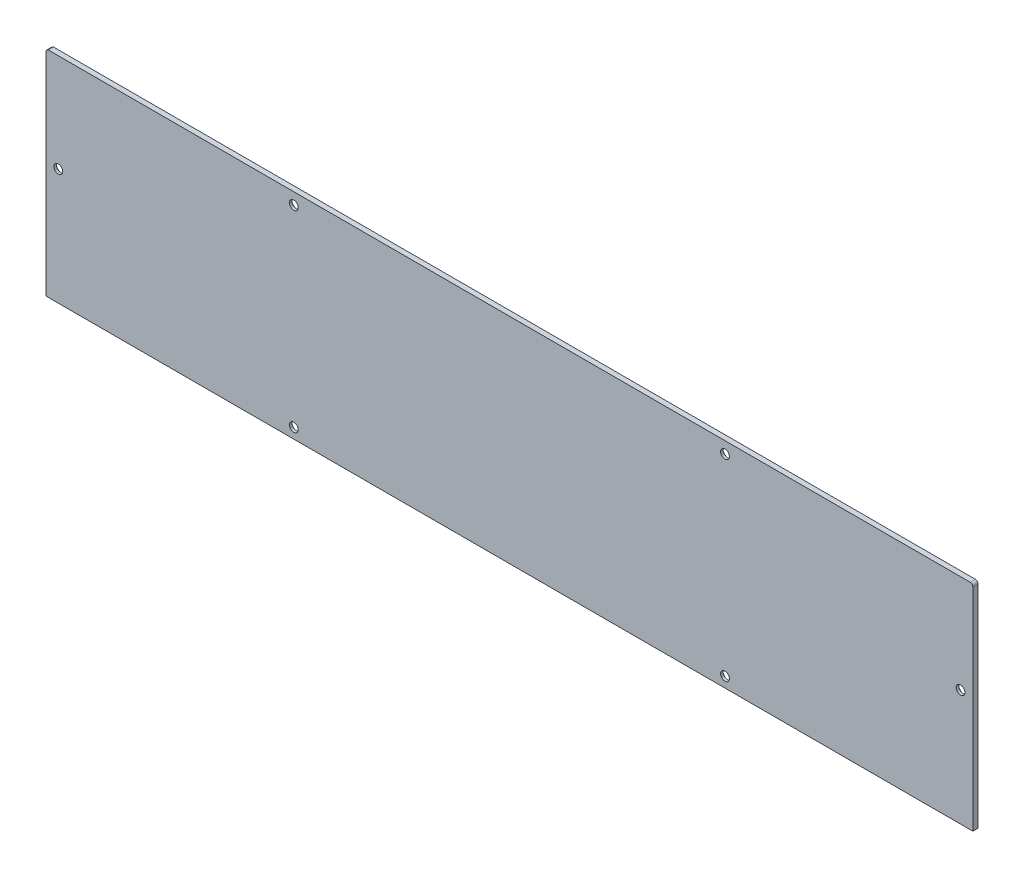
SolidWorks part; units mm, degrees
material "6061 合金"
ref_plane "前视基准面" through (0, 0, 0) normal (0, 0, 1) x (1, 0, 0)
ref_plane "上视基准面" through (0, 0, 0) normal (0, 1, 0) x (1, 0, 0)
ref_plane "右视基准面" through (0, 0, 0) normal (1, 0, 0) x (0, 0, -1)
sketch "草图1" plane through (0, 0, 222.7245) normal (0, 0, -1) x (-1, 0, 0)
  line L0 (282.7502, -10) -> (-76.2519, -10) construction
  line L1 (-76.2519, 70) -> (-76.2519, -2.5) construction
  line L2 (282.7502, -8.05) -> (282.7502, 70) construction
  line L4 (-76.2519, -10) -> (282.7502, -10)
  line L5 (282.7502, 70) -> (282.7502, -10)
  line L6 (279.7502, 73) -> (-73.2519, 73)
  line L7 (-76.2519, -10) -> (-76.2519, 70)
  arc A2 (282.7502, 70) -> (279.7502, 73) centre (279.7502, 70) ccw
  arc A3 (-73.2519, 73) -> (-76.2519, 70) centre (-73.2519, 70) ccw
  arc A4 (-73.2519, 73) -> (-76.2519, 70) centre (-73.2519, 70) ccw construction
  arc A5 (282.7502, 70) -> (279.7502, 73) centre (279.7502, 70) ccw construction
extrude "凸台-拉伸1" add sketch "草图1" along normal blind 2
sketch "草图2" plane through (0, 0, 220.7245) normal (0, 0, 1) x (1, 0, 0)
  line L0 (71.5019, 35) -> (71.5019, 68.5) construction
  line L1 (71.5019, 68.5) -> (-19.7492, 68.5) construction
  line L2 (-19.7492, 68.5) -> (-186.7492, 68.5) construction
  line L3 (-186.7492, 68.5) -> (-278.0002, 68.5) construction
  line L4 (-278.0002, 68.5) -> (-278.0002, 35) construction
  circle A1 centre (-19.7492, 68.5) radius 1.25 construction
  circle A4 centre (-278.0002, 35) radius 1.25
  circle A5 centre (-186.7492, 68.5) radius 1.25
  circle A6 centre (-19.7492, 68.5) radius 1.0541
  circle A7 centre (71.5019, 35) radius 1.25
  circle A11 centre (-278.0002, 35) radius 1.0974 construction
  circle A14 centre (71.5019, 35) radius 1.25 construction
hole_wizard "打孔尺寸(%根据)内六角圆柱头螺钉的类型2" positions "3D草图1" profile "草图3" counterbore size "M3" standard "GB"
sketch3d "3D草图1"
  point P0 (71.5019, 35, 220.7245)
  point P3 (-19.7492, 68.5, 220.7245)
  point P6 (-186.7492, 68.5, 220.7245)
  point P9 (-278.0002, 35, 220.7245)
sketch "草图3" plane through (71.5019, 35, 220.7245) normal (1, 0, 0) x (0, 1, 0)
  line L0 (0, 0) -> (0, 8.5215)
  line L1 (0, 8.5215) -> (1.7, 7.5)
  line L2 (1.7, 7.5) -> (1.7, 1)
  line L3 (1.7, 1) -> (3, 1)
  line L4 (3, 1) -> (3, 0)
  line L5 (3, 0) -> (0, 0)
  line L10 (0, 8.5215) -> (-1.7, 7.5) construction
  line L11 (0, -6.35) -> (0, 107.95) construction
  dimension "孔直径" = 3.4
  dimension "孔深度" = 7.5
  dimension "柱形沉头孔直径" = 6
  dimension "柱形沉头孔深度" = 1
  dimension "导头角度" = 118
sketch "草图4" plane through (0, 0, 220.7245) normal (0, 0, -1) x (-1, 0, 0)
  line L4 (-76.2519, 70) -> (-76.2519, -10)
  line L5 (-76.2519, -10) -> (282.7502, -10)
  line L6 (282.7502, -10) -> (282.7502, 70)
  line L7 (279.7502, 73) -> (-73.2519, 73)
  line L8 (-76.2519, 70) -> (-76.2519, -10)
  line L10 (282.7502, -10) -> (282.7502, 70)
  line L11 (279.7502, 73) -> (-73.2519, 73)
  line L13 (282.2502, -10) -> (282.2502, 70)
  line L14 (279.7502, 72.5) -> (-73.2519, 72.5)
  line L15 (-75.7519, 70) -> (-75.7519, -10)
  line L16 (282.2502, -10) -> (282.7502, -10)
  line L17 (-76.2519, -10) -> (-75.7519, -10)
  arc A2 (282.7502, 70) -> (279.7502, 73) centre (279.7502, 70) ccw
  arc A3 (-73.2519, 73) -> (-76.2519, 70) centre (-73.2519, 70) ccw
  arc A4 (282.7502, 70) -> (279.7502, 73) centre (279.7502, 70) ccw
  arc A5 (-73.2519, 73) -> (-76.2519, 70) centre (-73.2519, 70) ccw
  arc A6 (282.2502, 70) -> (279.7502, 72.5) centre (279.7502, 70) ccw
  arc A8 (-73.2519, 72.5) -> (-75.7519, 70) centre (-73.2519, 70) ccw
  dimension "D1" = 0
  dimension "D3" = 0.5
extrude "切除-拉伸1" cut sketch "草图4" against normal through all
hole_wizard "打孔尺寸(%根据)内六角圆柱头螺钉的类型2" positions "3D草图2" profile "草图5" counterbore size "M3" standard "GB"
sketch3d "3D草图2"
  point P0 (-19.7492, -6, 195.7245)
  point P3 (-186.7492, -6, 195.7245)
sketch "草图5" plane through (-19.7492, -6, 220.7245) normal (1, 0, 0) x (0, 1, 0)
  line L0 (0, 0) -> (0, 20.5215)
  line L1 (0, 20.5215) -> (1.7, 19.5)
  line L2 (1.7, 19.5) -> (1.7, 1)
  line L3 (1.7, 1) -> (3, 1)
  line L4 (3, 1) -> (3, 0)
  line L5 (3, 0) -> (0, 0)
  line L6 (0, 20.5215) -> (-1.7, 19.5) construction
  line L7 (0, -6.35) -> (0, 107.95) construction
  dimension "孔直径" = 3.4
  dimension "孔深度" = 19.5
  dimension "柱形沉头孔直径" = 6
  dimension "柱形沉头孔深度" = 1
  dimension "导头角度" = 118
sketch "草图6" plane through (0, 0, 220.7245) normal (0, 0, -1) x (-1, 0, 0)
  line L0 (-76.2519, 72) -> (-76.2519, -10)
  line L2 (282.7502, -10) -> (282.7502, 72)
  line L3 (281.7502, 73) -> (-75.2519, 73)
  line L4 (282.2502, -10) -> (282.2502, 70)
  line L5 (279.7502, 72.5) -> (-73.2519, 72.5)
  line L6 (-75.7519, 70) -> (-75.7519, -10)
  line L7 (-75.7519, -10) -> (282.2502, -10)
  line L8 (282.2502, -10) -> (282.2502, 70)
  line L9 (279.7502, 72.5) -> (-73.2519, 72.5)
  line L10 (-75.7519, 70) -> (-75.7519, -10)
  line L12 (-75.7519, -10) -> (282.2502, -10) construction
  line L13 (-76.2519, -10.5) -> (282.7502, -10.5) construction
  line L14 (-75.7519, -10) -> (-76.2519, -10)
  line L15 (282.2502, -10) -> (282.7502, -10)
  line L16 (279.7502, 73) -> (-73.2519, 73) construction
  line L17 (282.7502, -10.5) -> (282.7502, 70) construction
  line L18 (-76.2519, 70) -> (-76.2519, -10.5) construction
  arc A2 (282.2502, 70) -> (279.7502, 72.5) centre (279.7502, 70) ccw
  arc A3 (-73.2519, 72.5) -> (-75.7519, 70) centre (-73.2519, 70) ccw
  arc A4 (282.2502, 70) -> (279.7502, 72.5) centre (279.7502, 70) ccw
  arc A5 (-73.2519, 72.5) -> (-75.7519, 70) centre (-73.2519, 70) ccw
  arc A6 (282.7502, 72) -> (281.7502, 73) centre (281.7502, 72) ccw
  arc A7 (-76.2519, 72) -> (-75.2519, 73) centre (-75.2519, 72) cw
  arc A8 (-73.2519, 73) -> (-76.2519, 70) centre (-73.2519, 70) ccw construction
  arc A9 (282.7502, 70) -> (279.7502, 73) centre (279.7502, 70) ccw construction
  dimension "D3" = 1
  dimension "D4" = 1
  dimension "D1" = 0
  dimension "D2" = 0.5
extrude "凸台-拉伸3" add sketch "草图6" against normal up to surface (2 mm away) up to face at (-21.4492, -6, 222.7245)
